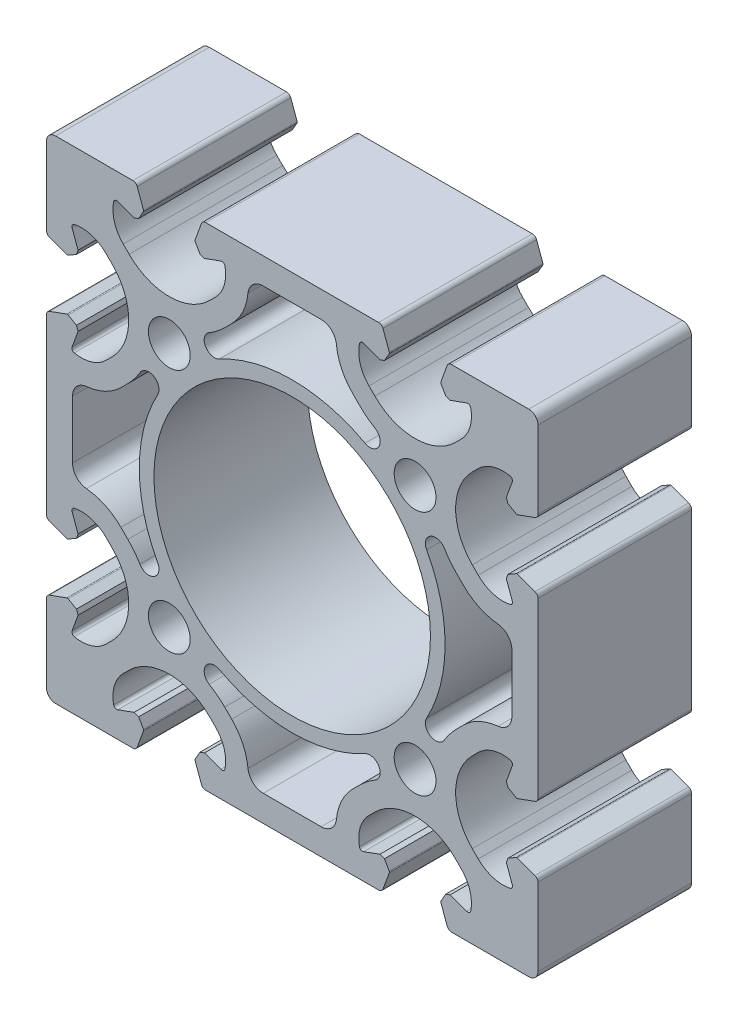
SolidWorks part; units mm, degrees
material "6005-T5"
ref_plane "Front" through (0, 0, 0) normal (0, 0, 1) x (1, 0, 0)
ref_plane "Top" through (0, 0, 0) normal (0, 1, 0) x (1, 0, 0)
ref_plane "Right" through (0, 0, 0) normal (1, 0, 0) x (0, 0, -1)
sketch "Sk Main Extrusion" plane through (0, 0, 0) normal (0, 0, 1) x (1, 0, 0)
  line L0 (10.9844, 26.7344) -> (9.8486, 27.8702)
  line L5 (4.7083, 35.75) -> (-4.7083, 35.75)
  line L6 (-9.8486, 27.8702) -> (-10.9844, 26.7344)
  line L7 (-35.75, 4.7083) -> (-35.75, -4.7083)
  line L8 (-27.8702, -9.8486) -> (-26.7344, -10.9844)
  line L9 (-26.7344, 10.9844) -> (-27.8702, 9.8486)
  line L10 (26.7344, -10.9844) -> (27.8702, -9.8486)
  line L11 (35.75, -4.7083) -> (35.75, 4.7083)
  line L12 (27.8702, 9.8486) -> (26.7344, 10.9844)
  line L13 (-10.9844, -26.7344) -> (-9.8486, -27.8702)
  line L14 (-4.7083, -35.75) -> (4.7083, -35.75)
  line L15 (9.8486, -27.8702) -> (10.9844, -26.7344)
  line L16 (-36.6712, -24.1901) -> (-39.5065, -25.2221)
  line L17 (-40, -25.9268) -> (-40, -38.5)
  line L18 (-38.5, -40) -> (-25.9268, -40)
  line L19 (-25.2221, -39.5065) -> (-24.1901, -36.6712)
  line L20 (-24.2085, -36.4607) -> (-24.9876, -35.1113)
  line L21 (-24.9876, -35.1113) -> (-25.7185, -34.8453)
  line L22 (-25.7185, -34.8453) -> (-28.3962, -35.8198)
  line L23 (-27.5042, -30.2727) -> (-26.5407, -29.3093)
  line L24 (-13.4593, -29.3093) -> (-12.4958, -30.2727)
  line L25 (-11.6038, -35.8198) -> (-14.2815, -34.8453)
  line L26 (-14.2815, -34.8453) -> (-15.0124, -35.1113)
  line L27 (-15.0124, -35.1113) -> (-15.7915, -36.4607)
  line L28 (-15.8099, -36.6712) -> (-14.7779, -39.5065)
  line L29 (-14.0732, -40) -> (14.0732, -40)
  line L30 (14.7779, -39.5065) -> (15.8099, -36.6712)
  line L31 (15.7915, -36.4607) -> (15.0124, -35.1113)
  line L32 (15.0124, -35.1113) -> (14.2815, -34.8453)
  line L33 (14.2815, -34.8453) -> (11.6038, -35.8198)
  line L34 (12.4958, -30.2727) -> (13.4593, -29.3093)
  line L35 (26.5407, -29.3093) -> (27.5042, -30.2727)
  line L36 (28.3962, -35.8198) -> (25.7185, -34.8453)
  line L37 (25.7185, -34.8453) -> (24.9876, -35.1113)
  line L38 (24.9876, -35.1113) -> (24.2085, -36.4607)
  line L39 (24.1901, -36.6712) -> (25.2221, -39.5065)
  line L40 (25.9268, -40) -> (38.5, -40)
  line L41 (40, -38.5) -> (40, -25.9268)
  line L42 (39.5065, -25.2221) -> (36.6712, -24.1901)
  line L43 (36.4607, -24.2085) -> (35.1113, -24.9876)
  line L44 (35.1113, -24.9876) -> (34.8453, -25.7185)
  line L45 (34.8453, -25.7185) -> (35.8198, -28.3962)
  line L46 (30.2727, -27.5042) -> (29.3093, -26.5407)
  line L47 (29.3093, -13.4593) -> (30.2727, -12.4958)
  line L48 (35.8198, -11.6038) -> (34.8453, -14.2815)
  line L49 (34.8453, -14.2815) -> (35.1113, -15.0124)
  line L50 (35.1113, -15.0124) -> (36.4607, -15.7915)
  line L51 (36.6712, -15.8099) -> (39.5065, -14.7779)
  line L52 (40, -14.0732) -> (40, 14.0732)
  line L53 (39.5065, 14.7779) -> (36.6712, 15.8099)
  line L54 (36.4607, 15.7915) -> (35.1113, 15.0124)
  line L55 (35.1113, 15.0124) -> (34.8453, 14.2815)
  line L56 (34.8453, 14.2815) -> (35.8198, 11.6038)
  line L57 (30.2727, 12.4958) -> (29.3093, 13.4593)
  line L58 (29.3093, 26.5407) -> (30.2727, 27.5042)
  line L59 (35.8198, 28.3962) -> (34.8453, 25.7185)
  line L60 (34.8453, 25.7185) -> (35.1113, 24.9876)
  line L61 (35.1113, 24.9876) -> (36.4607, 24.2085)
  line L62 (36.6712, 24.1901) -> (39.5065, 25.2221)
  line L63 (40, 25.9268) -> (40, 38.5)
  line L64 (38.5, 40) -> (25.9268, 40)
  line L65 (25.2221, 39.5065) -> (24.1901, 36.6712)
  line L66 (24.2085, 36.4607) -> (24.9876, 35.1113)
  line L67 (24.9876, 35.1113) -> (25.7185, 34.8453)
  line L68 (25.7185, 34.8453) -> (28.3962, 35.8198)
  line L69 (27.5042, 30.2727) -> (26.5407, 29.3093)
  line L70 (13.4593, 29.3093) -> (12.4958, 30.2727)
  line L71 (11.6038, 35.8198) -> (14.2815, 34.8453)
  line L72 (14.2815, 34.8453) -> (15.0124, 35.1113)
  line L73 (15.0124, 35.1113) -> (15.7915, 36.4607)
  line L74 (15.8099, 36.6712) -> (14.7779, 39.5065)
  line L75 (14.0732, 40) -> (-14.0732, 40)
  line L76 (-14.7779, 39.5065) -> (-15.8099, 36.6712)
  line L77 (-15.7915, 36.4607) -> (-15.0124, 35.1113)
  line L78 (-15.0124, 35.1113) -> (-14.2815, 34.8453)
  line L79 (-14.2815, 34.8453) -> (-11.6038, 35.8198)
  line L80 (-12.4958, 30.2727) -> (-13.4593, 29.3093)
  line L81 (-26.5407, 29.3093) -> (-27.5042, 30.2727)
  line L82 (-28.3962, 35.8198) -> (-25.7185, 34.8453)
  line L83 (-25.7185, 34.8453) -> (-24.9876, 35.1113)
  line L84 (-24.9876, 35.1113) -> (-24.2085, 36.4607)
  line L85 (-24.1901, 36.6712) -> (-25.2221, 39.5065)
  line L86 (-25.9268, 40) -> (-38.5, 40)
  line L87 (-40, 38.5) -> (-40, 25.9268)
  line L88 (-39.5065, 25.2221) -> (-36.6712, 24.1901)
  line L89 (-36.4607, 24.2085) -> (-35.1113, 24.9876)
  line L90 (-35.1113, 24.9876) -> (-34.8453, 25.7185)
  line L91 (-34.8453, 25.7185) -> (-35.8198, 28.3962)
  line L92 (-30.2727, 27.5042) -> (-29.3093, 26.5407)
  line L93 (-29.3093, 13.4593) -> (-30.2727, 12.4958)
  line L94 (-35.8198, 11.6038) -> (-34.8453, 14.2815)
  line L95 (-34.8453, 14.2815) -> (-35.1113, 15.0124)
  line L96 (-35.1113, 15.0124) -> (-36.4607, 15.7915)
  line L97 (-36.6712, 15.8099) -> (-39.5065, 14.7779)
  line L98 (-40, 14.0732) -> (-40, -14.0732)
  line L99 (-39.5065, -14.7779) -> (-36.6712, -15.8099)
  line L100 (-36.4607, -15.7915) -> (-35.1113, -15.0124)
  line L101 (-35.1113, -15.0124) -> (-34.8453, -14.2815)
  line L102 (-34.8453, -14.2815) -> (-35.8198, -11.6038)
  line L103 (-30.2727, -12.4958) -> (-29.3093, -13.4593)
  line L104 (-29.3093, -26.5407) -> (-30.2727, -27.5042)
  line L105 (-35.8198, -28.3962) -> (-34.8453, -25.7185)
  line L106 (-34.8453, -25.7185) -> (-35.1113, -24.9876)
  line L107 (-35.1113, -24.9876) -> (-36.4607, -24.2085)
  arc A0 (-13.5061, 24.7777) -> (-11.8613, 21.8755) centre (-12.6565, 23.342) ccw
  arc A1 (11.8613, 21.8755) -> (-11.8613, 21.8755) centre (0, 0) ccw
  arc A2 (11.8613, 21.8755) -> (13.5061, 24.7777) centre (12.6565, 23.342) ccw
  arc A3 (10.9844, 26.7344) -> (13.5061, 24.7777) centre (20, 35.75) ccw
  arc A4 (7.1967, 33.4905) -> (9.8486, 27.8702) centre (16.354, 34.3755) ccw
  arc A5 (7.1967, 33.4905) -> (4.7083, 35.75) centre (4.7083, 33.25) ccw
  arc A6 (-4.7083, 35.75) -> (-7.1967, 33.4905) centre (-4.7083, 33.25) ccw
  arc A7 (-9.8486, 27.8702) -> (-7.1967, 33.4905) centre (-16.354, 34.3755) ccw
  arc A8 (-13.5061, 24.7777) -> (-10.9844, 26.7344) centre (-20, 35.75) ccw
  circle A9 centre (20, -20) radius 3.4
  circle A10 centre (-20, -20) radius 3.4
  circle A11 centre (-20, 20) radius 3.4
  circle A12 centre (20, 20) radius 3.4
  arc A13 (-33.4905, 7.1967) -> (-27.8702, 9.8486) centre (-34.3755, 16.354) ccw
  arc A14 (-33.4905, 7.1967) -> (-35.75, 4.7083) centre (-33.25, 4.7083) ccw
  arc A15 (-35.75, -4.7083) -> (-33.4905, -7.1967) centre (-33.25, -4.7083) ccw
  arc A16 (-27.8702, -9.8486) -> (-33.4905, -7.1967) centre (-34.3755, -16.354) ccw
  arc A17 (-24.7777, -13.5061) -> (-26.7344, -10.9844) centre (-35.75, -20) ccw
  arc A18 (-24.7777, -13.5061) -> (-21.8755, -11.8613) centre (-23.342, -12.6565) ccw
  arc A19 (-21.8755, 11.8613) -> (-21.8755, -11.8613) centre (0, 0) ccw
  arc A20 (-21.8755, 11.8613) -> (-24.7777, 13.5061) centre (-23.342, 12.6565) ccw
  arc A21 (-26.7344, 10.9844) -> (-24.7777, 13.5061) centre (-35.75, 20) ccw
  arc A22 (24.7777, 13.5061) -> (21.8755, 11.8613) centre (23.342, 12.6565) ccw
  arc A23 (21.8755, -11.8613) -> (21.8755, 11.8613) centre (0, 0) ccw
  arc A24 (21.8755, -11.8613) -> (24.7777, -13.5061) centre (23.342, -12.6565) ccw
  arc A25 (26.7344, -10.9844) -> (24.7777, -13.5061) centre (35.75, -20) ccw
  arc A26 (33.4905, -7.1967) -> (27.8702, -9.8486) centre (34.3755, -16.354) ccw
  arc A27 (33.4905, -7.1967) -> (35.75, -4.7083) centre (33.25, -4.7083) ccw
  arc A28 (35.75, 4.7083) -> (33.4905, 7.1967) centre (33.25, 4.7083) ccw
  arc A29 (27.8702, 9.8486) -> (33.4905, 7.1967) centre (34.3755, 16.354) ccw
  arc A30 (24.7777, 13.5061) -> (26.7344, 10.9844) centre (35.75, 20) ccw
  arc A31 (-11.8613, -21.8755) -> (-13.5061, -24.7777) centre (-12.6565, -23.342) ccw
  arc A32 (-10.9844, -26.7344) -> (-13.5061, -24.7777) centre (-20, -35.75) ccw
  arc A33 (-7.1967, -33.4905) -> (-9.8486, -27.8702) centre (-16.354, -34.3755) ccw
  arc A34 (-7.1967, -33.4905) -> (-4.7083, -35.75) centre (-4.7083, -33.25) ccw
  arc A35 (4.7083, -35.75) -> (7.1967, -33.4905) centre (4.7083, -33.25) ccw
  arc A36 (-39.5065, -25.2221) -> (-40, -25.9268) centre (-39.25, -25.9268) ccw
  arc A37 (-40, -38.5) -> (-38.5, -40) centre (-38.5, -38.5) ccw
  arc A38 (-25.9268, -40) -> (-25.2221, -39.5065) centre (-25.9268, -39.25) ccw
  arc A39 (-24.1901, -36.6712) -> (-24.2085, -36.4607) centre (-24.425, -36.5857) ccw
  arc A40 (-29.057, -35.4507) -> (-28.3962, -35.8198) centre (-28.5672, -35.35) ccw
  arc A41 (-27.5042, -30.2727) -> (-29.057, -35.4507) centre (-23.4737, -34.3032) ccw
  arc A42 (-13.4593, -29.3093) -> (-26.5407, -29.3093) centre (-20, -35.85) ccw
  arc A43 (-10.943, -35.4507) -> (-12.4958, -30.2727) centre (-16.5263, -34.3032) ccw
  arc A44 (-11.6038, -35.8198) -> (-10.943, -35.4507) centre (-11.4328, -35.35) ccw
  arc A45 (-15.7915, -36.4607) -> (-15.8099, -36.6712) centre (-15.575, -36.5857) ccw
  arc A46 (-14.7779, -39.5065) -> (-14.0732, -40) centre (-14.0732, -39.25) ccw
  arc A47 (14.0732, -40) -> (14.7779, -39.5065) centre (14.0732, -39.25) ccw
  arc A48 (15.8099, -36.6712) -> (15.7915, -36.4607) centre (15.575, -36.5857) ccw
  arc A49 (10.943, -35.4507) -> (11.6038, -35.8198) centre (11.4328, -35.35) ccw
  arc A50 (12.4958, -30.2727) -> (10.943, -35.4507) centre (16.5263, -34.3032) ccw
  arc A51 (26.5407, -29.3093) -> (13.4593, -29.3093) centre (20, -35.85) ccw
  arc A52 (29.057, -35.4507) -> (27.5042, -30.2727) centre (23.4737, -34.3032) ccw
  arc A53 (28.3962, -35.8198) -> (29.057, -35.4507) centre (28.5672, -35.35) ccw
  arc A54 (24.2085, -36.4607) -> (24.1901, -36.6712) centre (24.425, -36.5857) ccw
  arc A55 (25.2221, -39.5065) -> (25.9268, -40) centre (25.9268, -39.25) ccw
  arc A56 (38.5, -40) -> (40, -38.5) centre (38.5, -38.5) ccw
  arc A57 (40, -25.9268) -> (39.5065, -25.2221) centre (39.25, -25.9268) ccw
  arc A58 (36.6712, -24.1901) -> (36.4607, -24.2085) centre (36.5857, -24.425) ccw
  arc A59 (35.4507, -29.057) -> (35.8198, -28.3962) centre (35.35, -28.5672) ccw
  arc A60 (30.2727, -27.5042) -> (35.4507, -29.057) centre (34.3032, -23.4737) ccw
  arc A61 (29.3093, -13.4593) -> (29.3093, -26.5407) centre (35.85, -20) ccw
  arc A62 (35.4507, -10.943) -> (30.2727, -12.4958) centre (34.3032, -16.5263) ccw
  arc A63 (35.8198, -11.6038) -> (35.4507, -10.943) centre (35.35, -11.4328) ccw
  arc A64 (36.4607, -15.7915) -> (36.6712, -15.8099) centre (36.5857, -15.575) ccw
  arc A65 (39.5065, -14.7779) -> (40, -14.0732) centre (39.25, -14.0732) ccw
  arc A66 (40, 14.0732) -> (39.5065, 14.7779) centre (39.25, 14.0732) ccw
  arc A67 (36.6712, 15.8099) -> (36.4607, 15.7915) centre (36.5857, 15.575) ccw
  arc A68 (35.4507, 10.943) -> (35.8198, 11.6038) centre (35.35, 11.4328) ccw
  arc A69 (30.2727, 12.4958) -> (35.4507, 10.943) centre (34.3032, 16.5263) ccw
  arc A70 (29.3093, 26.5407) -> (29.3093, 13.4593) centre (35.85, 20) ccw
  arc A71 (35.4507, 29.057) -> (30.2727, 27.5042) centre (34.3032, 23.4737) ccw
  arc A72 (35.8198, 28.3962) -> (35.4507, 29.057) centre (35.35, 28.5672) ccw
  arc A73 (36.4607, 24.2085) -> (36.6712, 24.1901) centre (36.5857, 24.425) ccw
  arc A74 (39.5065, 25.2221) -> (40, 25.9268) centre (39.25, 25.9268) ccw
  arc A75 (40, 38.5) -> (38.5, 40) centre (38.5, 38.5) ccw
  arc A76 (25.9268, 40) -> (25.2221, 39.5065) centre (25.9268, 39.25) ccw
  arc A77 (24.1901, 36.6712) -> (24.2085, 36.4607) centre (24.425, 36.5857) ccw
  arc A78 (29.057, 35.4507) -> (28.3962, 35.8198) centre (28.5672, 35.35) ccw
  arc A79 (27.5042, 30.2727) -> (29.057, 35.4507) centre (23.4737, 34.3032) ccw
  arc A80 (13.4593, 29.3093) -> (26.5407, 29.3093) centre (20, 35.85) ccw
  arc A81 (10.943, 35.4507) -> (12.4958, 30.2727) centre (16.5263, 34.3032) ccw
  arc A82 (11.6038, 35.8198) -> (10.943, 35.4507) centre (11.4328, 35.35) ccw
  arc A83 (15.7915, 36.4607) -> (15.8099, 36.6712) centre (15.575, 36.5857) ccw
  arc A84 (14.7779, 39.5065) -> (14.0732, 40) centre (14.0732, 39.25) ccw
  arc A85 (-14.0732, 40) -> (-14.7779, 39.5065) centre (-14.0732, 39.25) ccw
  arc A86 (-15.8099, 36.6712) -> (-15.7915, 36.4607) centre (-15.575, 36.5857) ccw
  arc A87 (-10.943, 35.4507) -> (-11.6038, 35.8198) centre (-11.4328, 35.35) ccw
  arc A88 (-12.4958, 30.2727) -> (-10.943, 35.4507) centre (-16.5263, 34.3032) ccw
  arc A89 (-26.5407, 29.3093) -> (-13.4593, 29.3093) centre (-20, 35.85) ccw
  arc A90 (-29.057, 35.4507) -> (-27.5042, 30.2727) centre (-23.4737, 34.3032) ccw
  arc A91 (-28.3962, 35.8198) -> (-29.057, 35.4507) centre (-28.5672, 35.35) ccw
  arc A92 (-24.2085, 36.4607) -> (-24.1901, 36.6712) centre (-24.425, 36.5857) ccw
  arc A93 (-25.2221, 39.5065) -> (-25.9268, 40) centre (-25.9268, 39.25) ccw
  arc A94 (-38.5, 40) -> (-40, 38.5) centre (-38.5, 38.5) ccw
  arc A95 (-40, 25.9268) -> (-39.5065, 25.2221) centre (-39.25, 25.9268) ccw
  arc A96 (-36.6712, 24.1901) -> (-36.4607, 24.2085) centre (-36.5857, 24.425) ccw
  arc A97 (-35.4507, 29.057) -> (-35.8198, 28.3962) centre (-35.35, 28.5672) ccw
  arc A98 (-30.2727, 27.5042) -> (-35.4507, 29.057) centre (-34.3032, 23.4737) ccw
  arc A99 (-29.3093, 13.4593) -> (-29.3093, 26.5407) centre (-35.85, 20) ccw
  arc A100 (-35.4507, 10.943) -> (-30.2727, 12.4958) centre (-34.3032, 16.5263) ccw
  arc A101 (-35.8198, 11.6038) -> (-35.4507, 10.943) centre (-35.35, 11.4328) ccw
  arc A102 (-36.4607, 15.7915) -> (-36.6712, 15.8099) centre (-36.5857, 15.575) ccw
  arc A103 (-39.5065, 14.7779) -> (-40, 14.0732) centre (-39.25, 14.0732) ccw
  arc A104 (-40, -14.0732) -> (-39.5065, -14.7779) centre (-39.25, -14.0732) ccw
  arc A105 (-36.6712, -15.8099) -> (-36.4607, -15.7915) centre (-36.5857, -15.575) ccw
  arc A106 (-35.4507, -10.943) -> (-35.8198, -11.6038) centre (-35.35, -11.4328) ccw
  arc A107 (-30.2727, -12.4958) -> (-35.4507, -10.943) centre (-34.3032, -16.5263) ccw
  arc A108 (-29.3093, -26.5407) -> (-29.3093, -13.4593) centre (-35.85, -20) ccw
  arc A109 (-35.4507, -29.057) -> (-30.2727, -27.5042) centre (-34.3032, -23.4737) ccw
  arc A110 (-35.8198, -28.3962) -> (-35.4507, -29.057) centre (-35.35, -28.5672) ccw
  arc A111 (-36.4607, -24.2085) -> (-36.6712, -24.1901) centre (-36.5857, -24.425) ccw
  arc A112 (9.8486, -27.8702) -> (7.1967, -33.4905) centre (16.354, -34.3755) ccw
  arc A113 (13.5061, -24.7777) -> (10.9844, -26.7344) centre (20, -35.75) ccw
  arc A114 (13.5061, -24.7777) -> (11.8613, -21.8755) centre (12.6565, -23.342) ccw
  arc A115 (-11.8613, -21.8755) -> (11.8613, -21.8755) centre (0, 0) ccw
  circle A116 centre (0, 0) radius 22.5
extrude "Main Extrusion" add sketch "Sk Main Extrusion" against normal blind 25
sketch "Threaded Insert Mate Sketch" plane through (0, 0, 0) normal (0, 0, 1) x (1, 0, 0)
  line L0 (0, 22.5) -> (0, -22.5) construction
  line L1 (-22.5, 0) -> (22.5, 0) construction
  circle A0 centre (-20, 32.7) radius 5.6515
  circle A1 centre (-20, 20) radius 3.4 construction
  circle A2 centre (-7.3, 20) radius 5.6515
  circle A3 centre (-20, 7.3) radius 5.6515
  circle A4 centre (-32.7, 20) radius 5.6515
  circle A5 centre (0, 0) radius 22.5 construction
  circle A6 centre (32.7, 20) radius 5.6515
  circle A7 centre (20, 32.7) radius 5.6515
  circle A8 centre (20, -32.7) radius 5.6515
  circle A9 centre (32.7, -20) radius 5.6515
  circle A10 centre (-32.7, -20) radius 5.6515
  circle A11 centre (-20, -32.7) radius 5.6515
  point P13 (-20, 20)
  point P24 (20, 20)
  point P33 (20, -20)
  point P34 (-20, -20)
  dimension "D2" = 11.303
  dimension "D1" = 12.7
  dimension "D3" = 4
equation "\"Weight kg\"= round ( \"SW-Mass\" , 2 )"
equation "\"Weight lbs\"= round ( \"SW-Mass\" * 2.2046 , 2 )"
equation "\"Length mm\"= round ( \"Length@Main Extrusion\" , 2 )"
equation "\"Length in\"= round ( \"Length@Main Extrusion\" / 25.4 , 3 )"
